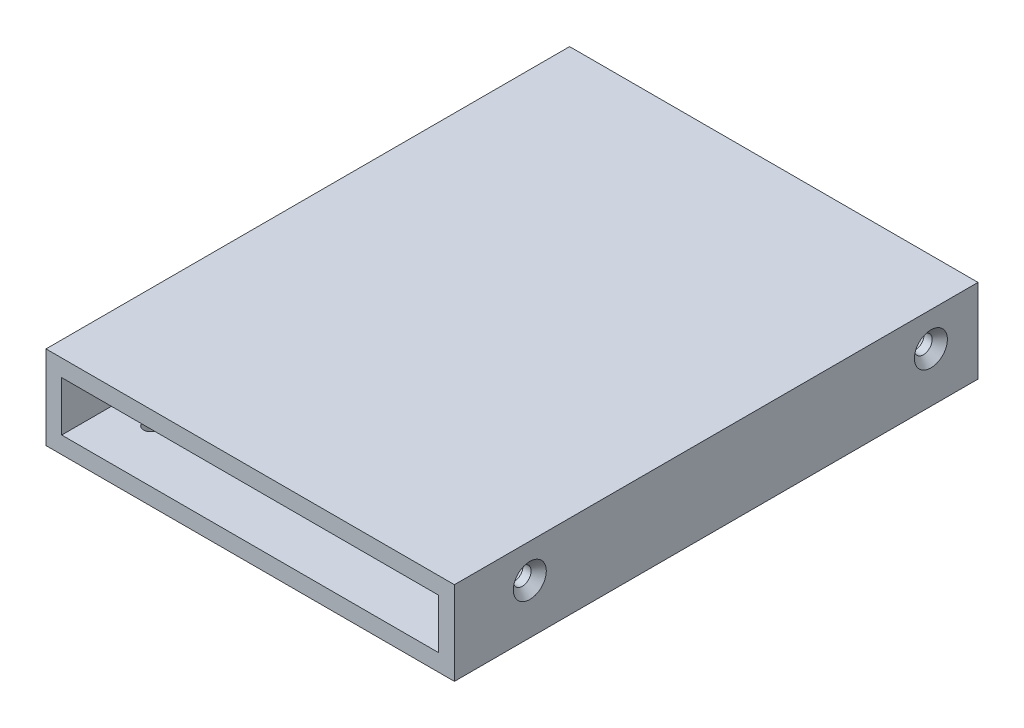
SolidWorks part; units mm, degrees
ref_plane "Plan de face" through (0, 0, 0) normal (0, 0, 1) x (1, 0, 0)
ref_plane "Plan de dessus" through (0, 0, 0) normal (0, 1, 0) x (1, 0, 0)
ref_plane "Plan de droite" through (0, 0, 0) normal (1, 0, 0) x (0, 0, -1)
sketch "Main-Sketch" plane through (0, 0, 0) normal (0, 0, 1) x (1, 0, 0)
  line L1 (0, 0) -> (78, 0)
  line L2 (0, 0) -> (0, 16)
  line L3 (0, 16) -> (78, 16)
  line L4 (78, 0) -> (78, 16)
  line L5 (3, 12.75) -> (75, 12.75)
  line L6 (3, 12.75) -> (3, 3.25)
  line L7 (3, 3.25) -> (75, 3.25)
  line L8 (75, 12.75) -> (75, 3.25)
  point P9 (39, 12.75)
  point P10 (39, 16)
  point P11 (3, 8)
  point P12 (0, 8)
  dimension "D1" = 78
  dimension "D2" = 16
  dimension "D3" = 72
  dimension "D4" = 9.5
extrude "Main-Extrusion" add sketch "Main-Sketch" along normal blind 100
hole_wizard "Fraisage pour vis à tête fraisée M31" positions "Esquisse3" profile "Esquisse4" countersink size "M3" standard "Ansi Metric" end condition through all
sketch "Esquisse3" plane through (0, 0, 0) normal (-1, 0, 0) x (0, 0, 1)
  line L0 (100, 0) -> (0, 0) construction
  line L1 (0, 16) -> (0, 0) construction
  point P0 (9, 9.5)
  dimension "D1" = 9.5
  dimension "D2" = 9
sketch "Esquisse4" plane through (0, 9.5, 9) normal (0, 1, 0) x (0, 0, 1)
  line L0 (0, 0) -> (0, 78)
  line L1 (0, 78) -> (1.7, 78)
  line L2 (1.7, 78) -> (1.7, 1.45)
  line L3 (1.7, 1.45) -> (3.15, 0)
  line L5 (3.15, 0) -> (0, 0)
  line L6 (-1.7, 1.45) -> (-3.15, 0) construction
  line L11 (0, -6.35) -> (0, 107.95) construction
  dimension "Diamètre du perçage jusqu'au prochain" = 3.4
  dimension "Profondeur du perçage jusqu'au prochain" = 78
  dimension "Diamètre du fraisage entrant" = 6.3
  dimension "Angle du fraisage entrant" = 90
pattern_linear "Répétition linéaire1" count 2 spacing 76.6 along (0, 0, 1) of "Fraisage pour vis à tête fraisée M31"
hole_wizard "Fraisage pour vis à tête fraisée M32" positions "Esquisse7" profile "Esquisse8" countersink size "M3" standard "Ansi Metric" end condition through all
sketch "Esquisse7" plane through (78, 0, 0) normal (1, 0, 0) x (0, 0, -1)
  point P0 (-85.6, 9.5)
sketch "Esquisse8" plane through (78, 9.5, 85.6) normal (0, 1, 0) x (0, 0, -1)
  line L0 (0, 0) -> (0, 154.5)
  line L1 (0, 154.5) -> (1.7, 154.5)
  line L2 (1.7, 154.5) -> (1.7, 1.45)
  line L3 (1.7, 1.45) -> (3.15, 0)
  line L5 (3.15, 0) -> (0, 0)
  line L6 (-1.7, 1.45) -> (-3.15, 0) construction
  line L11 (0, -6.35) -> (0, 107.95) construction
  dimension "Diamètre du perçage jusqu'au prochain" = 3.4
  dimension "Profondeur du perçage jusqu'au prochain" = 154.5
  dimension "Diamètre du fraisage entrant" = 6.3
  dimension "Angle du fraisage entrant" = 90
pattern_linear "Répétition linéaire3" count 2 spacing 76.5 along (1, 0, 0) of "Fraisage pour vis à tête fraisée M32"
hole_wizard "Fraisage pour vis à tête fraisée M33" positions "Esquisse9" profile "Esquisse10" countersink size "M3" standard "Ansi Metric" end condition through all
sketch "Esquisse9" plane through (78, 0, 0) normal (1, 0, 0) x (0, 0, -1)
  point P0 (-9, 9.5)
  point P3 (0, 0)
sketch "Esquisse10" plane through (78, 9.5, 9) normal (0, 1, 0) x (0, 0, -1)
  line L0 (0, 0) -> (0, 78)
  line L1 (0, 78) -> (1.7, 78)
  line L2 (1.7, 78) -> (1.7, 1.45)
  line L3 (1.7, 1.45) -> (3.15, 0)
  line L5 (3.15, 0) -> (0, 0)
  line L6 (-1.7, 1.45) -> (-3.15, 0) construction
  line L11 (0, -6.35) -> (0, 107.95) construction
  dimension "Diamètre du perçage jusqu'au prochain" = 3.4
  dimension "Profondeur du perçage jusqu'au prochain" = 78
  dimension "Diamètre du fraisage entrant" = 6.3
  dimension "Angle du fraisage entrant" = 90
sketch "Support-Fix-Sketch" plane through (0, 0, 0) normal (0, -1, 0) x (1, 0, 0)
  line L0 (0, 100) -> (0, 0) construction
  line L1 (78, 100) -> (78, 0) construction
  line L2 (0, 0) -> (78, 0) construction
  line L3 (0, 100) -> (78, 100) construction
  circle A0 centre (68, 90) radius 1.35
  circle A1 centre (68, 10) radius 1.35
  circle A2 centre (10, 10) radius 1.35
  circle A3 centre (10, 90) radius 1.35
  dimension "D1" = 2.7
  dimension "D2" = 10
  dimension "D3" = 10
  dimension "D4" = 10
  dimension "D5" = 10
  dimension "D6" = 58
  dimension "D7" = 80
extrude "Support-Fix-Hole" cut sketch "Support-Fix-Sketch" against normal up to next
